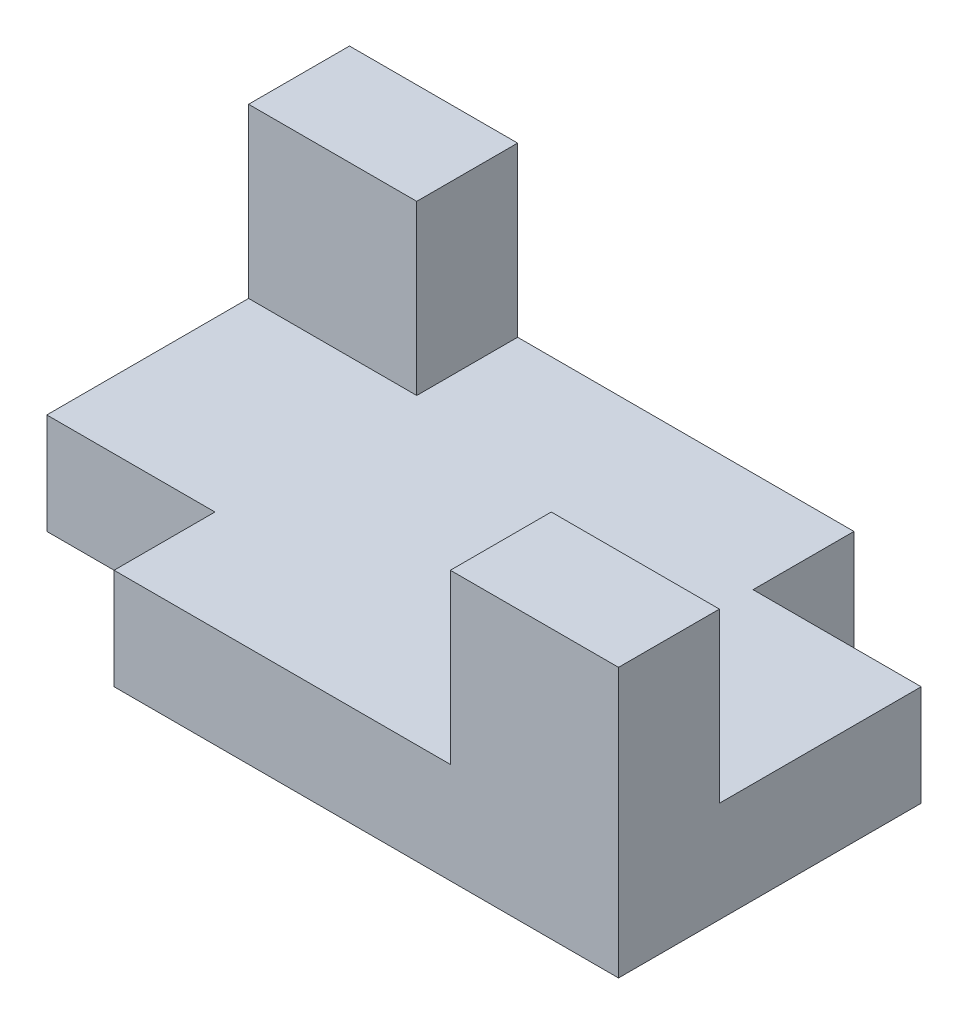
SolidWorks part; units mm, degrees
ref_plane "Front Plane" through (0, 0, 0) normal (0, 0, 1) x (1, 0, 0)
ref_plane "Top Plane" through (0, 0, 0) normal (0, 1, 0) x (1, 0, 0)
ref_plane "Right Plane" through (0, 0, 0) normal (1, 0, 0) x (0, 0, -1)
sketch "Sketch2" plane through (0, 0, 0) normal (0, 1, 0) x (1, 0, 0)
  line L1 (-47.3187, 28.626) -> (52.6813, 28.626)
  line L2 (-47.3187, 28.626) -> (-47.3187, -31.374)
  line L3 (-47.3187, -31.374) -> (52.6813, -31.374)
  line L4 (52.6813, 28.626) -> (52.6813, -31.374)
  point P20 (-47.3187, -1.374)
  dimension "D1" = 100
  dimension "D2" = 60
extrude "Boss-Extrude1" add sketch "Sketch2" along normal blind 15
sketch "Sketch3" plane through (0, 15, 0) normal (0, 1, 0) x (1, 0, 0)
  line L1 (-22.3187, 13.626) -> (-47.3187, 13.626)
  line L2 (-22.3187, 13.626) -> (-22.3187, 28.626)
  line L3 (-22.3187, 28.626) -> (-47.3187, 28.626)
  line L4 (-47.3187, 13.626) -> (-47.3187, 28.626)
  dimension "D1" = 15
  dimension "D2" = 25
extrude "Boss-Extrude2" add sketch "Sketch3" along normal blind 25 contours L2 L1 L4 L3
sketch "Sketch4" plane through (0, 15, 0) normal (0, 1, 0) x (1, 0, 0)
  line L1 (27.6813, -16.374) -> (52.6813, -16.374)
  line L2 (27.6813, -16.374) -> (27.6813, -31.374)
  line L3 (27.6813, -31.374) -> (52.6813, -31.374)
  line L4 (52.6813, -16.374) -> (52.6813, -31.374)
  dimension "D1" = 25
  dimension "D2" = 15
extrude "Boss-Extrude3" add sketch "Sketch4" along normal blind 25
sketch "Sketch5" plane through (0, 15, 0) normal (0, 1, 0) x (1, 0, 0)
  line L1 (-22.3187, -16.374) -> (-47.3187, -16.374)
  line L2 (-22.3187, -16.374) -> (-22.3187, -31.374)
  line L3 (-22.3187, -31.374) -> (-47.3187, -31.374)
  line L4 (-47.3187, -16.374) -> (-47.3187, -31.374)
  dimension "D1" = 15
  dimension "D2" = 25
extrude "Cut-Extrude1" cut sketch "Sketch5" against normal blind 15
sketch "Sketch6" plane through (0, 15, 0) normal (0, 1, 0) x (1, 0, 0)
  line L1 (27.6813, 13.626) -> (52.6813, 13.626)
  line L2 (27.6813, 13.626) -> (27.6813, 28.626)
  line L3 (27.6813, 28.626) -> (52.6813, 28.626)
  line L4 (52.6813, 13.626) -> (52.6813, 28.626)
  dimension "D1" = 25
  dimension "D2" = 15
extrude "Cut-Extrude2" cut sketch "Sketch6" against normal blind 15
